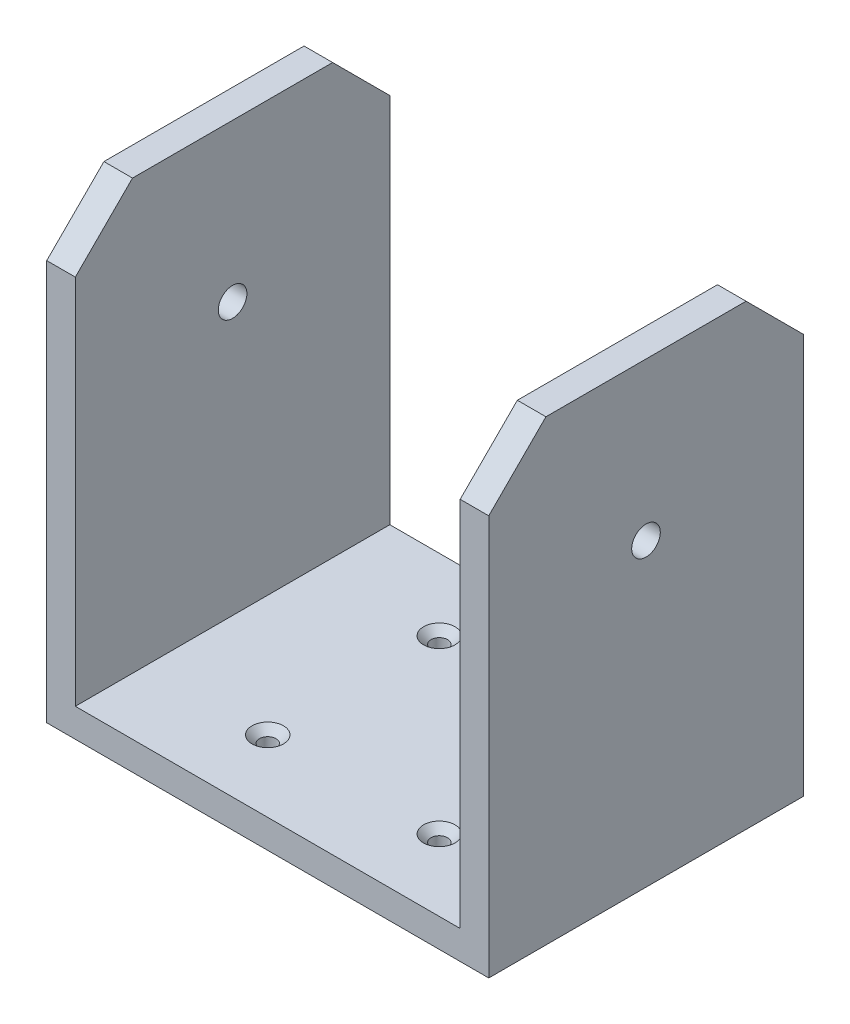
SolidWorks part; units mm, degrees
ref_plane "Ön Düzlem" through (0, 0, 0) normal (0, 0, 1) x (1, 0, 0)
ref_plane "Üst Düzlem" through (0, 0, 0) normal (0, 1, 0) x (1, 0, 0)
ref_plane "Sağ Düzlem" through (0, 0, 0) normal (1, 0, 0) x (0, 0, -1)
sketch "Sketch1" plane through (0, 0, 0) normal (1, 0, 0) x (0, 0, -1)
  line L0 (-27.5, 17.5) -> (-17.5, 27.5)
  line L1 (-17.5, 27.5) -> (17.5, 27.5)
  line L2 (-27.5, 17.5) -> (-27.5, -27.5)
  line L3 (-27.5, -27.5) -> (27.5, -27.5)
  line L4 (27.5, 17.5) -> (27.5, -27.5)
  line L5 (-22.5, 22.5) -> (27.5, -27.5) construction
  line L6 (-27.5, -27.5) -> (22.5, 22.5) construction
  line L7 (17.5, 27.5) -> (27.5, 17.5)
  circle A0 centre (0, 0) radius 2.5
  point P0 (0, 0)
  dimension "D1" = 5
  dimension "D3" = 45
  dimension "D4" = 45
extrude "Boss-Extrude1" add sketch "Sketch1" along normal blind 5
sketch "Sketch2" plane through (0, -27.5, 0) normal (0, -1, 0) x (1, 0, 0)
  line L1 (0, 27.5) -> (5, 27.5)
  line L2 (0, 27.5) -> (0, -27.5)
  line L3 (0, -27.5) -> (5, -27.5)
  line L4 (5, 27.5) -> (5, -27.5)
extrude "Boss-Extrude2" add sketch "Sketch2" along normal blind 25
sketch "Sketch3" plane through (0, -52.5, 0) normal (0, -1, 0) x (1, 0, 0)
  line L1 (0, 27.5) -> (-72.3, 27.5)
  line L2 (0, 27.5) -> (0, -27.5)
  line L3 (0, -27.5) -> (-72.3, -27.5)
  line L4 (-72.3, 27.5) -> (-72.3, -27.5)
  dimension "D1" = 72.3
  dimension "D2" = 55
extrude "Boss-Extrude3" add sketch "Sketch3" against normal blind 5
sketch "Sketch4" plane through (-72.3, 0, 0) normal (-1, 0, 0) x (0, 0, 1)
  line L0 (-17.5, 27.5) -> (-27.5, 17.5)
  line L1 (-27.5, -47.5) -> (27.5, -47.5)
  line L2 (-27.5, -47.5) -> (-27.5, 17.5)
  line L3 (-17.5, 27.5) -> (17.5, 27.5)
  line L4 (27.5, -47.5) -> (27.5, 17.5)
  line L5 (17.5, 27.5) -> (27.5, 17.5)
extrude "Boss-Extrude4" add sketch "Sketch4" against normal blind 5
sketch "Sketch5" plane through (-67.3, 0, 0) normal (1, 0, 0) x (0, 0, -1)
  circle A0 centre (0, 0) radius 2.5
extrude "Cut-Extrude1" cut sketch "Sketch5" against normal up to next
hole_wizard "CSK for M2.5 Flat Head Machine Screw1" positions "Sketch7" profile "Sketch6" countersink size "M2.5" standard "ANSI Metric" end condition through all
sketch "Sketch7" plane through (0, -47.5, 0) normal (0, 1, 0) x (1, 0, 0)
  point P0 (-16.15, 15)
  point P3 (-16.15, -15)
  point P6 (-46.15, -15)
  point P9 (-46.15, 15)
sketch "Sketch6" plane through (-16.15, -47.5, -15) normal (1, 0, 0) x (0, 0, 1)
  line L0 (0, 0) -> (0, 5)
  line L1 (0, 5) -> (1.45, 5)
  line L2 (1.45, 5) -> (1.45, 1.3)
  line L3 (1.45, 1.3) -> (2.75, 0)
  line L5 (2.75, 0) -> (0, 0)
  line L6 (-1.45, 1.3) -> (-2.75, 0) construction
  line L11 (0, -6.35) -> (0, 107.95) construction
  dimension "Thru Hole Dia." = 2.9
  dimension "Thru Hole Depth" = 5
  dimension "Near C'Sink Dia." = 5.5
  dimension "Near C'Sink Angle" = 90
